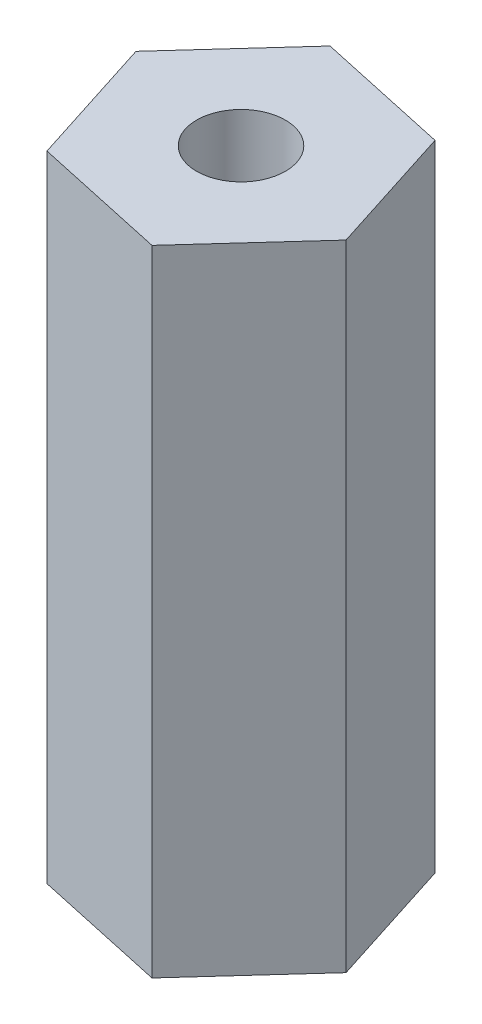
SolidWorks part; units mm, degrees
ref_plane "Front Plane" through (0, 0, 0) normal (0, 0, 1) x (1, 0, 0)
ref_plane "Top Plane" through (0, 0, 0) normal (0, 1, 0) x (1, 0, 0)
ref_plane "Right Plane" through (0, 0, 0) normal (1, 0, 0) x (0, 0, -1)
sketch "Sketch1" plane through (0, 0, 0) normal (0, 1, 0) x (1, 0, 0)
  line L1 (1.8496, 2.0346) -> (-0.8372, 2.6191)
  line L2 (-0.8372, 2.6191) -> (-2.6868, 0.5845)
  line L3 (-2.6868, 0.5845) -> (-1.8496, -2.0346)
  line L4 (-1.8496, -2.0346) -> (0.8372, -2.6191)
  line L5 (0.8372, -2.6191) -> (2.6868, -0.5845)
  line L6 (2.6868, -0.5845) -> (1.8496, 2.0346)
  circle A0 centre (0, 0) radius 2.3813 construction
  dimension "D1" = 4.7625
extrude "Boss-Extrude1" add sketch "Sketch1" along normal blind 12.7
hole_wizard "Tap Drill for #2-56 Tap1" positions "Sketch2" profile "Sketch3" hole size "#2-56" standard "ANSI Inch" end condition through all
sketch "Sketch2" plane through (0, 12.7, 0) normal (0, 1, 0) x (1, 0, 0)
  point P0 (0, 0)
sketch "Sketch3" plane through (0, 12.7, 0) normal (1, 0, 0) x (0, 0, 1)
  line L0 (0, 0) -> (0, 12.7)
  line L1 (0, 12.7) -> (0.889, 12.7)
  line L2 (0.889, 12.7) -> (0.889, 0)
  line L5 (0.889, 0) -> (0, 0)
  line L11 (0, -6.35) -> (0, 107.95) construction
  dimension "Thru Hole Dia." = 1.778
  dimension "Thru Hole Depth" = 12.7
